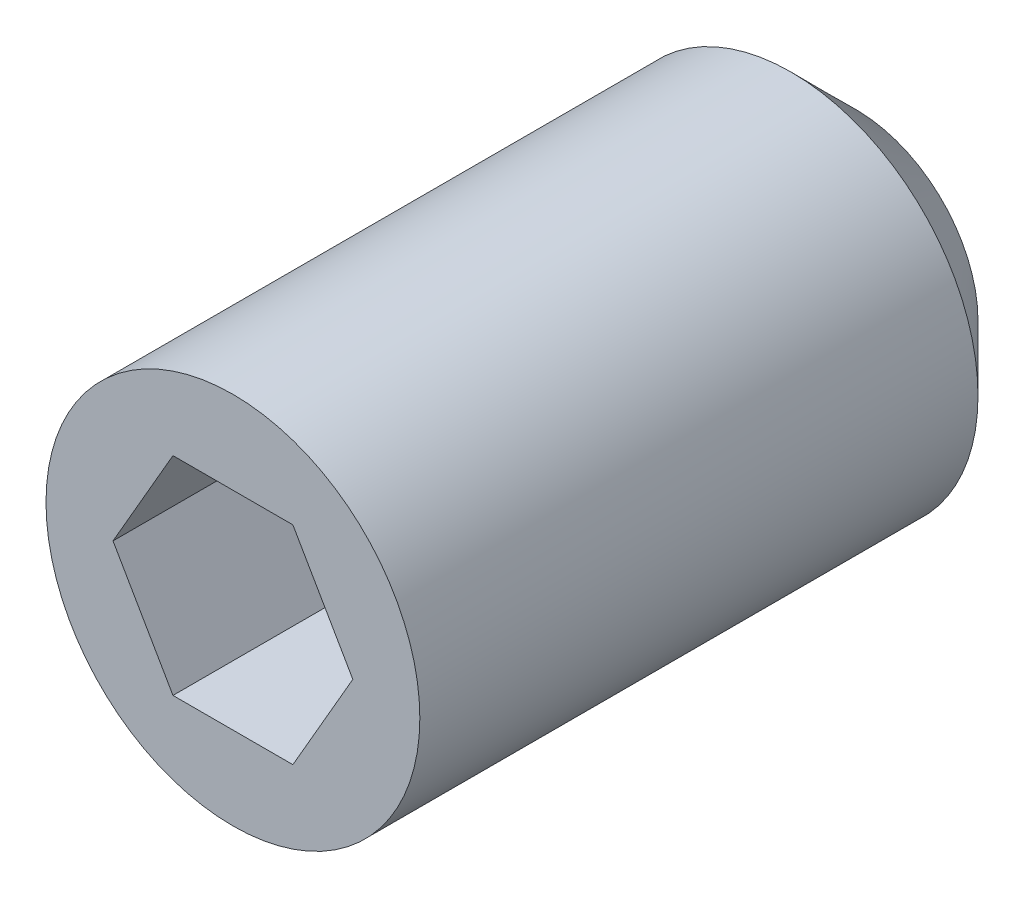
SolidWorks part; units mm, degrees
ref_plane "Front" through (0, 0, 0) normal (0, 0, 1) x (1, 0, 0)
ref_plane "Top" through (0, 0, 0) normal (0, 1, 0) x (1, 0, 0)
ref_plane "Right" through (0, 0, 0) normal (1, 0, 0) x (0, 0, -1)
sketch "Sketch1" plane through (0, 0, 0) normal (0, 0, 1) x (1, 0, 0)
  circle A0 centre (0, 0) radius 1.143
  dimension "D1" = 2.286
extrude "cylinder" add sketch "Sketch1" along normal blind 3.81
sketch "Hexagon - circumscribed1" plane through (0.0568, 0.0667, 3.81) normal (0, 0, 1) x (1, 0, 0)
  line L0 (-0.4235, 0.5683) -> (0.3098, 0.5683)
  line L1 (0.3098, 0.5683) -> (0.6764, -0.0667)
  line L2 (0.6764, -0.0667) -> (0.3098, -0.7017)
  line L3 (0.3098, -0.7017) -> (-0.4235, -0.7017)
  line L4 (-0.4235, -0.7017) -> (-0.7901, -0.0667)
  line L5 (-0.7901, -0.0667) -> (-0.4235, 0.5683)
  circle A0 centre (-0.0568, -0.0667) radius 0.635 construction
  circle A2 centre (-0.0568, -0.0667) radius 1.143 construction
  dimension "D1" = 1.27
extrude "hex" cut sketch "Hexagon - circumscribed1" against normal blind 1.5875
chamfer "Chamfer1" distance 0.3969 angle 45 1 edges at (1.143, 0, 0)
